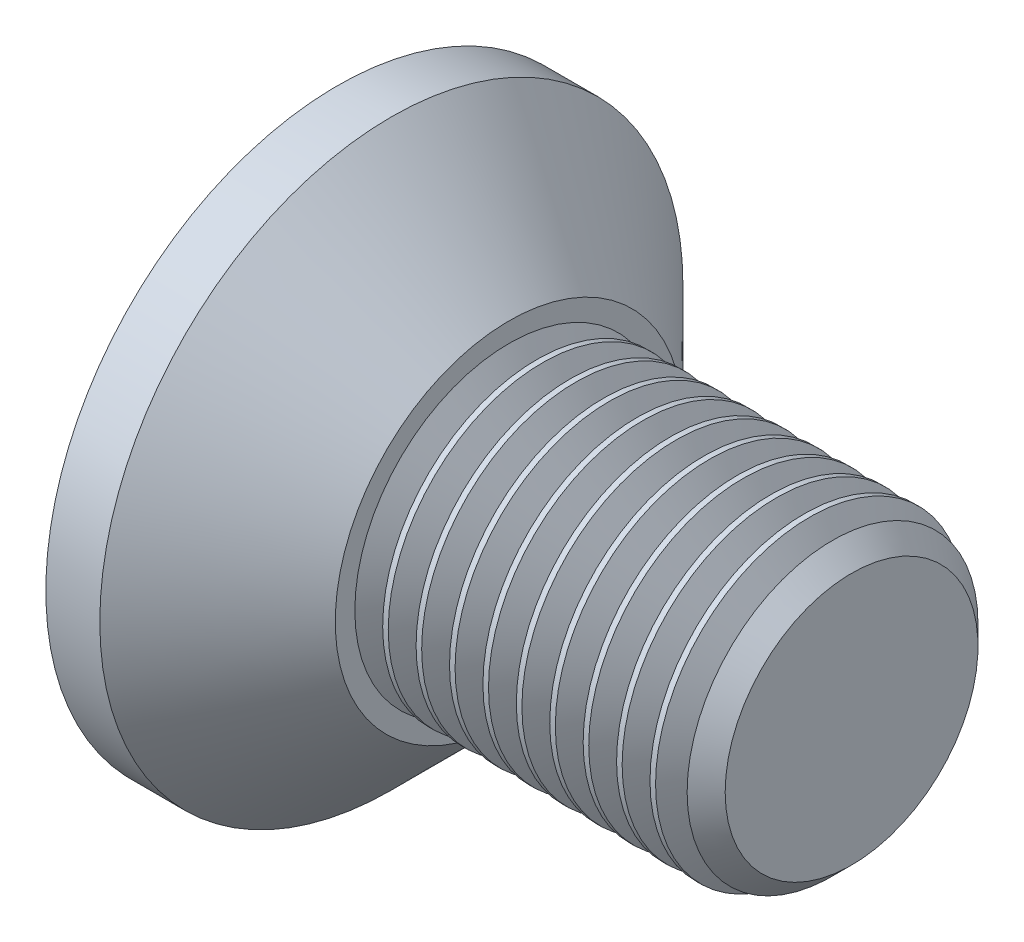
SolidWorks part; units mm, degrees
ref_plane "Front" through (0, 0, 0) normal (0, 0, 1) x (1, 0, 0)
ref_plane "Top" through (0, 0, 0) normal (0, 1, 0) x (1, 0, 0)
ref_plane "Right" through (0, 0, 0) normal (1, 0, 0) x (0, 0, -1)
sketch "Sketch1" plane through (0, 0, 0) normal (0, 0, 1) x (1, 0, 0)
  line L0 (0, 0) -> (0, 6.72)
  line L1 (0, 6.72) -> (3.72, 3)
  line L2 (3.72, 3) -> (10, 3)
  line L3 (10, 3) -> (10, 0)
  line L4 (10, 0) -> (0, 0)
  line L5 (-0.5871, 0) -> (5.4927, 0) construction
  dimension "D1" = 45
  dimension "l" = 10
  dimension "k" = 3.72
  dimension "d" = 6
revolve "Base" add sketch "Sketch1" angle 360 about L5
cosmetic thread "ThreadCosmetic1" [suppressed] parameters "b"=6.2, "D2"=4.917
sketch "Sketch2" plane through (0, 0, 0) normal (1, 0, 0) x (0, 0, -1)
  line L1 (2.3094, 0) -> (1.1547, 2)
  line L2 (1.1547, 2) -> (-1.1547, 2)
  line L3 (-1.1547, 2) -> (-2.3094, 0)
  line L4 (-2.3094, 0) -> (-1.1547, -2)
  line L5 (-1.1547, -2) -> (1.1547, -2)
  line L6 (1.1547, -2) -> (2.3094, 0)
  circle A0 centre (0, 0) radius 2 construction
  dimension "s" = 4
extrude "HexagonSocket" cut sketch "Sketch2" along normal blind 2.2
sketch "Sketch3" plane through (0, 0, 0) normal (0, 0, 1) x (1, 0, 0)
  line L0 (-0.4391, 0) -> (4.425, 0) construction
  line L1 (2.2, 0) -> (2.2, -2) construction
  line L2 (2.2, 2) -> (3.3547, 0)
  line L3 (3.3547, 0) -> (2.2, -2) construction
  line L4 (2.2, 2) -> (2.2, 0)
  line L5 (2.2, 0) -> (3.3547, 0)
  line L7 (2.2, 2) -> (2.2, 0) construction
  dimension "D1" = 120
revolve "Cut-Revolve1" cut sketch "Sketch3" angle 360 about L0
fillet "HeadFillet" radius 0.25 1 edges at (3.72, 0, 3)
chamfer "Chamfer" distance 0.5415 angle 45 1 edges at (10, 0, 3)
sketch "Sketch4" plane through (0, 0, 0) normal (0, 1, 0) x (1, 0, 0)
  line L0 (11.8531, 0) -> (-2.694, 0) construction
  line L1 (-2, 10.67) -> (3, 10.67)
  line L2 (-2, 10.67) -> (-2, 5.67)
  line L3 (-2, 5.67) -> (3, 5.67)
  line L4 (3, 10.67) -> (3, 5.67)
  line L5 (0, 6.72) -> (0, -6.72) construction
  dimension "dk" = 11.34
  dimension "D2" = 2
  dimension "D3" = 5
  dimension "D4" = 5
revolve "Cut-Revolve2" cut sketch "Sketch4" angle 360 about L0
sketch "Sketch5" plane through (0, 0, 0) normal (0, 0, 1) x (1, 0, 0)
  line L0 (9.4585, 2.531) -> (9.7293, 3)
  line L1 (9.7293, 3) -> (9.7293, 3.5415)
  line L2 (9.7293, 3.5415) -> (9.1878, 3.5415)
  line L3 (9.1878, 3.5415) -> (9.1878, 3)
  line L4 (9.1878, 3) -> (9.4585, 2.531)
  line L5 (0, 0) -> (10.6885, 0) construction
  line L6 (9.4585, 3) -> (9.4585, -3) construction
  dimension "D1" = 6
  dimension "D2" = 0.5415
revolve "Cut-Revolve10" cut sketch "Sketch5" angle 360 about L5
pattern_linear "LPattern10" count 10 spacing 0.6498 along (-1, 0, 0) of "Cut-Revolve10"
equation "\"D1@Chamfer\" = (  \"d@Sketch1\" - \"D2@ThreadCosmetic1\" )  / 2"
equation "\"D1@Sketch5\" = \"d@Sketch1\""
equation "\"D2@Sketch5\" =  ( \"d@Sketch1\" - \"D2@ThreadCosmetic1\" )  / 2"
equation "\"D3@LPattern10\" = \"D2@Sketch5\" * 1.2"
equation "\"D1@LPattern10\" = \"b@ThreadCosmetic1\" / \"D3@LPattern10\""
